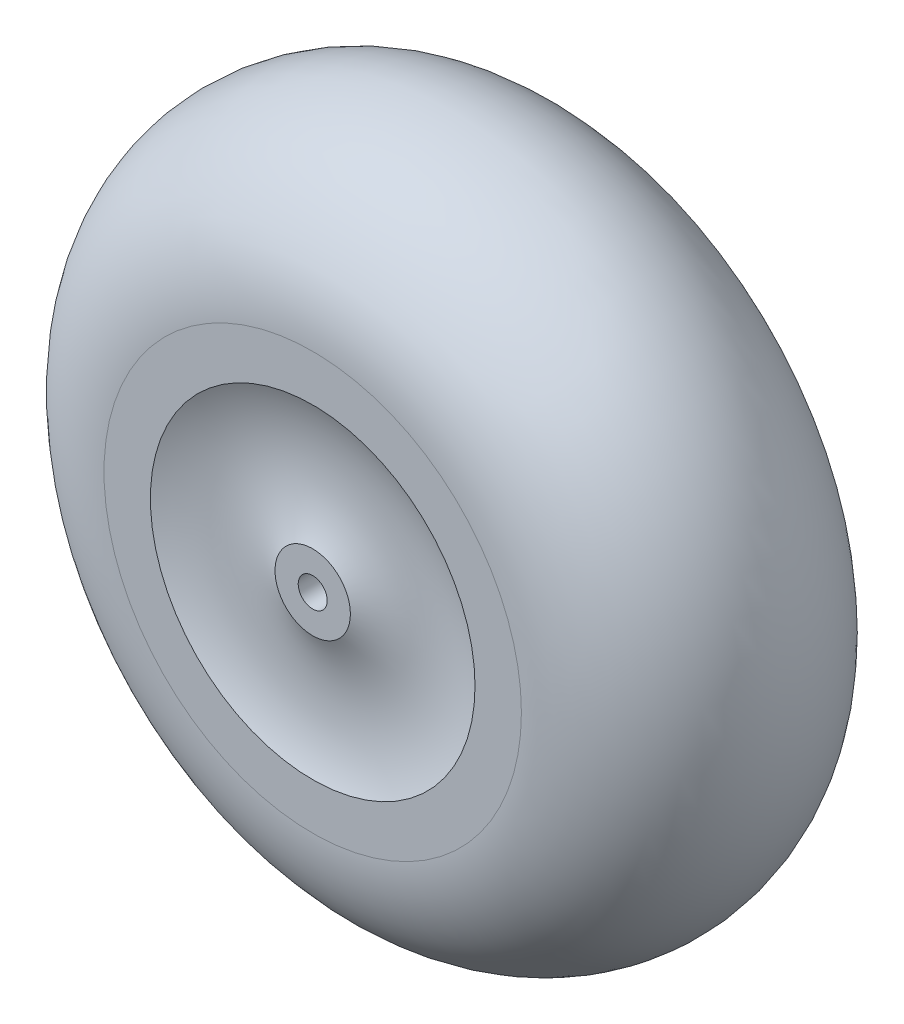
SolidWorks part; units mm, degrees
ref_plane "Front Plane" through (0, 0, 0) normal (0, 0, 1) x (1, 0, 0)
ref_plane "Top Plane" through (0, 0, 0) normal (0, 1, 0) x (1, 0, 0)
ref_plane "Right Plane" through (0, 0, 0) normal (1, 0, 0) x (0, 0, -1)
sketch "Sketch1" plane through (0, 0, 0) normal (0, 1, 0) x (1, 0, 0)
  line L0 (0, -25.4) -> (0, 25.4) construction
  line L1 (0, -25.4) -> (-7.9375, -25.4) construction
  line L2 (-7.9375, -25.4) -> (-7.9375, 25.4)
  line L3 (0, 0) -> (-7.9375, 0) construction
  line L4 (-7.9375, -25.4) -> (-20.6375, -25.4)
  line L5 (-7.9375, 25.4) -> (-20.6375, 25.4)
  line L6 (-20.6375, 25.4) -> (-20.6375, -19.05)
  line L7 (-88.9, -19.05) -> (-88.9, -25.4) construction
  line L8 (-88.9, -25.4) -> (-20.6375, -25.4) construction
  line L9 (-88.9, -25.4) -> (-114.3, -25.4)
  line L10 (-114.3, 50.8) -> (-114.3, -25.4) construction
  line L12 (-88.9, 127) -> (-88.9, -19.05)
  line L13 (-20.6375, -25.4) -> (-20.6375, -19.05) construction
  line L14 (-54.7688, -17.813) -> (-54.7688, -11.463) construction
  line L15 (-114.313, 127) -> (-88.9, 127)
  line L16 (-190.5, 50.7935) -> (-114.3, 50.8) construction
  arc A0 (-20.6375, -25.4) -> (-88.9, -25.4) centre (-54.7688, -98.3792) ccw
  arc A1 (-20.6375, -19.05) -> (-88.9, -19.05) centre (-54.7688, -92.0292) ccw
  arc A2 (-114.3, -25.4) -> (-114.313, 127) centre (-114.3, 50.8) cw
  point P4 (0, 0)
  point P19 (-190.5, 50.7935)
  dimension "D7" = 76.2
  dimension "D1" = 50.8
  dimension "D2" = 7.9375
  dimension "D3" = 12.7
  dimension "D4" = 190.5
  dimension "D5" = 6.35
  dimension "D6" = 25.4
revolve "Revolve1" add sketch "Sketch1" angle 360 about L0
